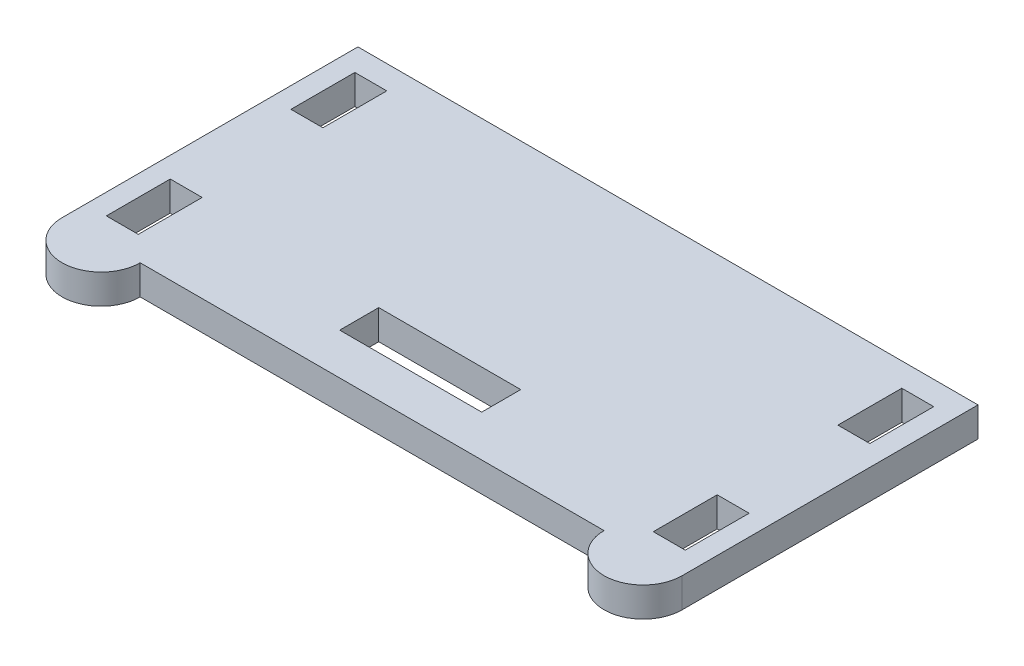
SolidWorks part; units mm, degrees
material "Custom Plastic"
ref_plane "Front Plane" through (0, 0, 0) normal (0, 0, 1) x (1, 0, 0)
ref_plane "Top Plane" through (0, 0, 0) normal (0, 1, 0) x (1, 0, 0)
ref_plane "Right Plane" through (0, 0, 0) normal (1, 0, 0) x (0, 0, -1)
sketch "Sketch1" plane through (0, 0, 0) normal (0, 1, 0) x (1, 0, 0)
  line L0 (0, 15.875) -> (0, -15.875) construction
  line L1 (-24.892, -15.875) -> (24.892, -15.875)
  line L2 (-33.274, -15.875) -> (-33.274, 15.875)
  line L3 (-33.274, 15.875) -> (33.274, 15.875)
  line L4 (33.274, -15.875) -> (33.274, 15.875)
  line L5 (-33.274, -15.875) -> (33.274, 15.875) construction
  line L6 (-33.274, 15.875) -> (33.274, -15.875) construction
  line L7 (31.0642, 13.335) -> (27.6352, 13.335)
  line L8 (31.0642, 13.335) -> (31.0642, 6.477)
  line L9 (31.0642, 6.477) -> (27.6352, 6.477)
  line L10 (27.6352, 13.335) -> (27.6352, 6.477)
  line L11 (31.0642, -6.477) -> (27.6352, -6.477)
  line L12 (31.0642, -6.477) -> (31.0642, -13.335)
  line L13 (31.0642, -13.335) -> (27.6352, -13.335)
  line L14 (27.6352, -6.477) -> (27.6352, -13.335)
  line L15 (-27.6352, -6.477) -> (-27.6352, -13.335)
  line L16 (-31.0642, -13.335) -> (-27.6352, -13.335)
  line L17 (-31.0642, -6.477) -> (-31.0642, -13.335)
  line L18 (-31.0642, -6.477) -> (-27.6352, -6.477)
  line L19 (-27.6352, 13.335) -> (-27.6352, 6.477)
  line L20 (-31.0642, 6.477) -> (-27.6352, 6.477)
  line L21 (-31.0642, 13.335) -> (-31.0642, 6.477)
  line L22 (-31.0642, 13.335) -> (-27.6352, 13.335)
  line L24 (-7.9248, -11.43) -> (7.3152, -11.43)
  line L25 (-7.9248, -11.43) -> (-7.9248, -7.239)
  line L26 (-7.9248, -7.239) -> (7.3152, -7.239)
  line L27 (7.3152, -11.43) -> (7.3152, -7.239)
  arc A0 (24.892, -15.875) -> (33.274, -15.875) centre (29.083, -15.875) ccw
  arc A1 (-24.892, -15.875) -> (-33.274, -15.875) centre (-29.083, -15.875) cw
  point P0 (0, 0)
  dimension "D13" = 4.191
  dimension "D1" = 66.548
  dimension "D2" = 31.75
  dimension "D3" = 2.2098
  dimension "D4" = 2.54
  dimension "D5" = 3.429
  dimension "D6" = 6.858
  dimension "D7" = 2.2098
  dimension "D8" = 2.54
  dimension "D9" = 4.445
  dimension "D10" = 15.24
  dimension "D11" = 4.191
  dimension "D12" = 20.32
extrude "Boss-Extrude1" add sketch "Sketch1" along normal blind 3.175
